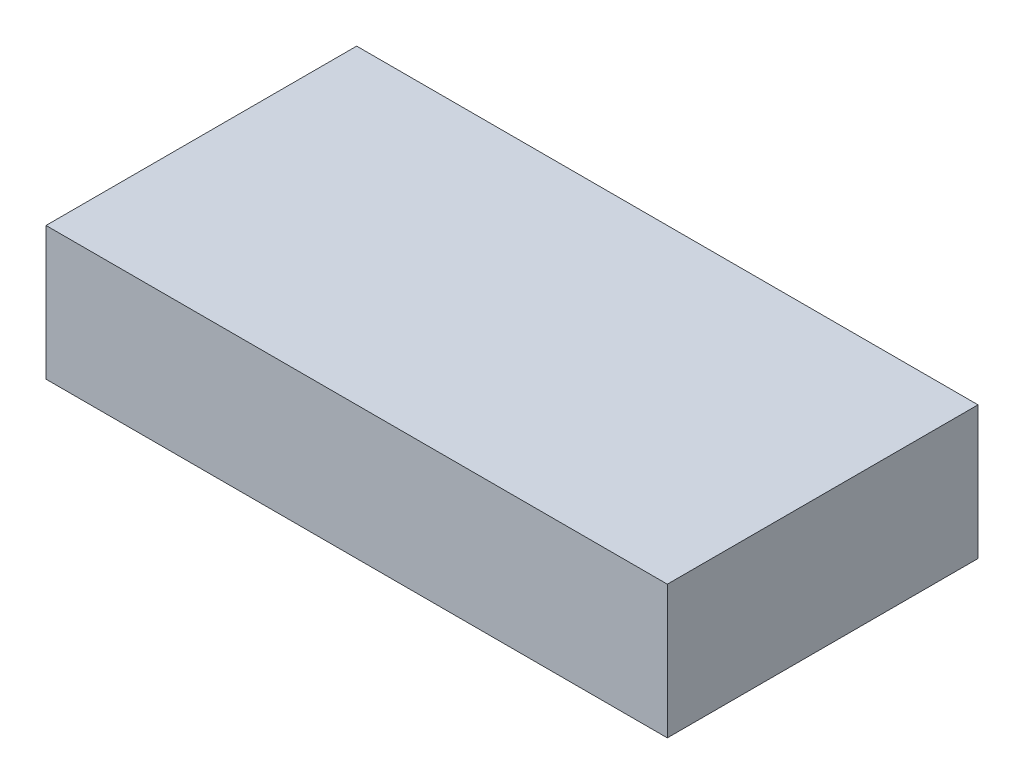
SolidWorks part; units mm, degrees
ref_plane "Front Plane" through (0, 0, 0) normal (0, 0, 1) x (1, 0, 0)
ref_plane "Top Plane" through (0, 0, 0) normal (0, 1, 0) x (1, 0, 0)
ref_plane "Right Plane" through (0, 0, 0) normal (1, 0, 0) x (0, 0, -1)
sketch "Sketch1" plane through (0, 0, 0) normal (0, 1, 0) x (1, 0, 0)
  line L1 (-35, 17.5) -> (35, 17.5)
  line L2 (-35, 17.5) -> (-35, -17.5)
  line L3 (-35, -17.5) -> (35, -17.5)
  line L4 (35, 17.5) -> (35, -17.5)
  line L5 (-35, 17.5) -> (35, -17.5) construction
  line L6 (-35, -17.5) -> (35, 17.5) construction
  point P0 (0, 0)
  dimension "D1" = 70
  dimension "D2" = 35
extrude "Boss-Extrude1" add sketch "Sketch1" along normal blind 15
